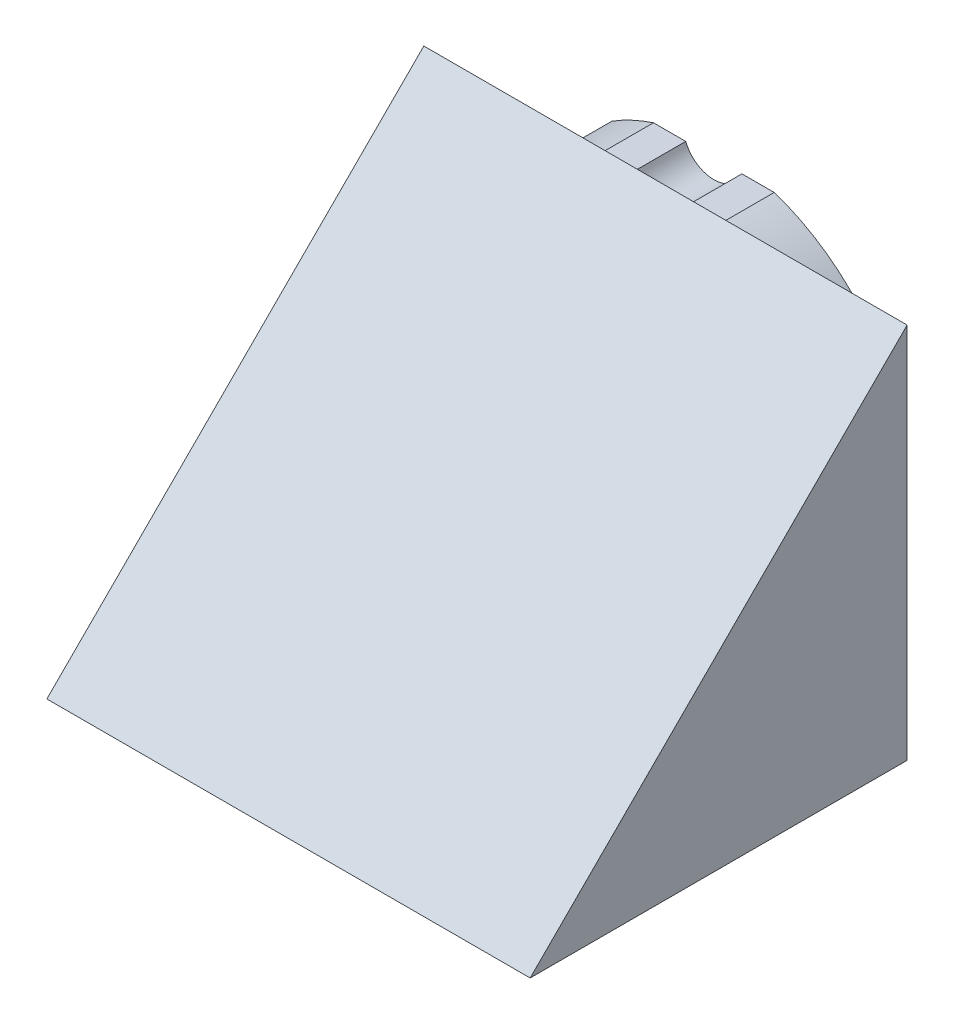
SolidWorks part; units mm, degrees
ref_plane "Piano frontale" through (0, 0, 0) normal (0, 0, 1) x (1, 0, 0)
ref_plane "Piano superiore" through (0, 0, 0) normal (0, 1, 0) x (1, 0, 0)
ref_plane "Piano destro" through (0, 0, 0) normal (1, 0, 0) x (0, 0, -1)
sketch "Schizzo4" plane through (0, 0, 0) normal (0, 0, 1) x (1, 0, 0)
  line L9 (-5.8114, 38) -> (-12.49, 38)
  line L10 (-21.0896, 33.9886) -> (-17.3224, 29.3364)
  line L11 (-17.6476, 26.2422) -> (-21.9996, 22.718)
  line L12 (-25.0938, 23.0432) -> (-28.8611, 27.6954)
  line L13 (-39.154, -8.1833) -> (-35.8146, -13.9673)
  line L14 (-30.0029, -24.0334) -> (-26.664, -29.8167)
  line L15 (26.664, -29.8167) -> (30.0029, -24.0334)
  line L16 (35.8146, -13.9673) -> (39.154, -8.1833)
  line L17 (12.49, 38) -> (5.8114, 38)
  line L18 (-5.8114, 38) -> (-12.49, 38)
  line L19 (-21.0896, 33.9886) -> (-17.3224, 29.3364)
  line L20 (-17.6476, 26.2422) -> (-21.9996, 22.718)
  line L21 (-25.0938, 23.0432) -> (-28.8611, 27.6954)
  line L22 (-39.154, -8.1833) -> (-35.8146, -13.9673)
  line L23 (-30.0029, -24.0334) -> (-26.664, -29.8167)
  line L24 (26.664, -29.8167) -> (30.0029, -24.0334)
  line L25 (35.8146, -13.9673) -> (39.154, -8.1833)
  line L26 (12.49, 38) -> (5.8114, 38)
  arc A0 (-35, -3.5) -> (-35, 3.5) centre (-35, 0) ccw construction
  arc A1 (-35, 3.5) -> (-35, -3.5) centre (-35, 0) ccw construction
  arc A2 (0, -39.25) -> (0, -30.75) centre (0, -35) ccw construction
  arc A3 (0, -30.75) -> (0, -39.25) centre (0, -35) ccw construction
  arc A4 (30.3, 13.25) -> (30.3, 21.75) centre (30.3, 17.5) ccw construction
  arc A5 (30.3, 21.75) -> (30.3, 13.25) centre (30.3, 17.5) ccw construction
  arc A6 (-35, -3.5) -> (-35, 3.5) centre (-35, 0) ccw
  arc A7 (-35, 3.5) -> (-35, -3.5) centre (-35, 0) ccw
  arc A8 (0, -39.25) -> (0, -30.75) centre (0, -35) ccw
  arc A9 (-12.49, 38) -> (-21.0896, 33.9886) centre (0, 0) ccw
  arc A10 (-17.6476, 26.2422) -> (-17.3224, 29.3364) centre (-19.0321, 27.9519) ccw
  arc A11 (-25.0938, 23.0432) -> (-21.9996, 22.718) centre (-23.3841, 24.4277) ccw
  arc A12 (-28.8611, 27.6954) -> (-39.154, -8.1833) centre (0, 0) ccw
  arc A13 (-30.0029, -24.0334) -> (-35.8146, -13.9673) centre (-34.9, -20.15) ccw
  arc A14 (-26.664, -29.8167) -> (26.664, -29.8167) centre (0, 0) ccw
  arc A15 (35.8146, -13.9673) -> (30.0029, -24.0334) centre (34.9, -20.15) ccw
  arc A16 (39.154, -8.1833) -> (12.49, 38) centre (0, 0) ccw
  arc A17 (-5.8114, 38) -> (5.8114, 38) centre (0, 40.3) ccw
  arc A18 (-12.49, 38) -> (-21.0896, 33.9886) centre (0, 0) ccw
  arc A19 (-17.6476, 26.2422) -> (-17.3224, 29.3364) centre (-19.0321, 27.9519) ccw
  arc A20 (-25.0938, 23.0432) -> (-21.9996, 22.718) centre (-23.3841, 24.4277) ccw
  arc A21 (-28.8611, 27.6954) -> (-39.154, -8.1833) centre (0, 0) ccw
  arc A22 (-30.0029, -24.0334) -> (-35.8146, -13.9673) centre (-34.9, -20.15) ccw
  arc A23 (-26.664, -29.8167) -> (26.664, -29.8167) centre (0, 0) ccw
  arc A24 (35.8146, -13.9673) -> (30.0029, -24.0334) centre (34.9, -20.15) ccw
  arc A25 (39.154, -8.1833) -> (12.49, 38) centre (0, 0) ccw
  arc A26 (-5.8114, 38) -> (5.8114, 38) centre (0, 40.3) ccw
  arc A27 (0, -30.75) -> (0, -39.25) centre (0, -35) ccw
  arc A28 (30.3, 13.25) -> (30.3, 21.75) centre (30.3, 17.5) ccw
  arc A29 (30.3, 21.75) -> (30.3, 13.25) centre (30.3, 17.5) ccw
  point P22 (0, 0)
  point P25 (0, 0)
  arc M19 (25, 27.067) -> (25, 22.933) centre (25, 25) cw
  arc M20 (25, 22.933) -> (25, 27.067) centre (25, 25) cw
  line M21 (-5.8114, 38) -> (-12.49, 38)
  arc M22 (-12.49, 38) -> (-21.0896, 33.9886) centre (0, 0) ccw
  line M23 (-21.0896, 33.9886) -> (-17.3224, 29.3364)
  arc M24 (-17.3224, 29.3364) -> (-17.6476, 26.2422) centre (-19.0321, 27.9519) cw
  line M25 (-17.6476, 26.2422) -> (-21.9996, 22.718)
  arc M26 (-21.9996, 22.718) -> (-25.0938, 23.0432) centre (-23.3841, 24.4277) cw
  line M27 (-25.0938, 23.0432) -> (-28.8611, 27.6954)
  arc M28 (-28.8611, 27.6954) -> (-39.154, -8.1833) centre (0, 0) ccw
  line M29 (-39.154, -8.1833) -> (-35.8146, -13.9673)
  arc M30 (-35.8146, -13.9673) -> (-30.0029, -24.0334) centre (-34.9, -20.15) cw
  line M31 (-30.0029, -24.0334) -> (-26.664, -29.8167)
  arc M32 (-26.664, -29.8167) -> (26.664, -29.8167) centre (0, 0) ccw
  line M33 (26.664, -29.8167) -> (30.0029, -24.0334)
  arc M34 (30.0029, -24.0334) -> (35.8146, -13.9673) centre (34.9, -20.15) cw
  line M35 (35.8146, -13.9673) -> (39.154, -8.1833)
  arc M36 (39.154, -8.1833) -> (12.49, 38) centre (0, 0) ccw
  line M37 (12.49, 38) -> (5.8114, 38)
  arc M38 (5.8114, 38) -> (-5.8114, 38) centre (0, 40.3) cw
  arc M39 (-9, -30.379) -> (-9, -33.621) centre (-9, -32) cw
  arc M40 (-9, -33.621) -> (-9, -30.379) centre (-9, -32) cw
  arc M41 (9, -30.379) -> (9, -33.621) centre (9, -32) cw
  arc M42 (9, -33.621) -> (9, -30.379) centre (9, -32) cw
  arc M43 (-30.3, 13.25) -> (-30.3, 21.75) centre (-30.3, 17.5) cw
  arc M44 (-30.3, 21.75) -> (-30.3, 13.25) centre (-30.3, 17.5) cw
  arc M45 (30.3, 13.25) -> (30.3, 21.75) centre (30.3, 17.5) cw
  arc M46 (30.3, 21.75) -> (30.3, 13.25) centre (30.3, 17.5) cw
  arc M47 (0, -39.25) -> (0, -30.75) centre (0, -35) cw
  arc M48 (0, -30.75) -> (0, -39.25) centre (0, -35) cw
  arc M49 (-35, 3.5) -> (-35, -3.5) centre (-35, 0) cw
  arc M50 (-35, -3.5) -> (-35, 3.5) centre (-35, 0) cw
  arc M51 (35, 3.5) -> (35, -3.5) centre (35, 0) cw
  arc M52 (35, -3.5) -> (35, 3.5) centre (35, 0) cw
  arc M53 (0, -27.5) -> (0, 27.5) centre (0, 0) cw
  arc M54 (0, 27.5) -> (0, -27.5) centre (0, 0) cw
  dimension "D1" = 0
extrude "Estrusione-Estrusione2" add sketch "Schizzo4" along normal blind 10 contours M49 M50 | M53 M54 | M38 M21 M22 M23 M24 M25 M26 M27 M28 M29 M30 M31 M32 M33 M34 M35 M36 M37 M40 M39 M42 M41 M44 M43 M46 M45 M48 M47 M50 M49 M52 M51 M54 M53 M20 M19 | M41 M42 | M39 M40 | M51 M52 | M19 M20
sketch "Schizzo5" plane through (0, 0, 0) normal (1, 0, 0) x (0, 0, -1)
  line L0 (-10, 38) -> (-10, -40)
  line L1 (-10, -40) -> (-88, -40)
  line L2 (-88, -40) -> (-10, 38)
  dimension "D1" = 45
extrude "Estrusione-Estrusione3" add sketch "Schizzo5" along normal mid plane 100
